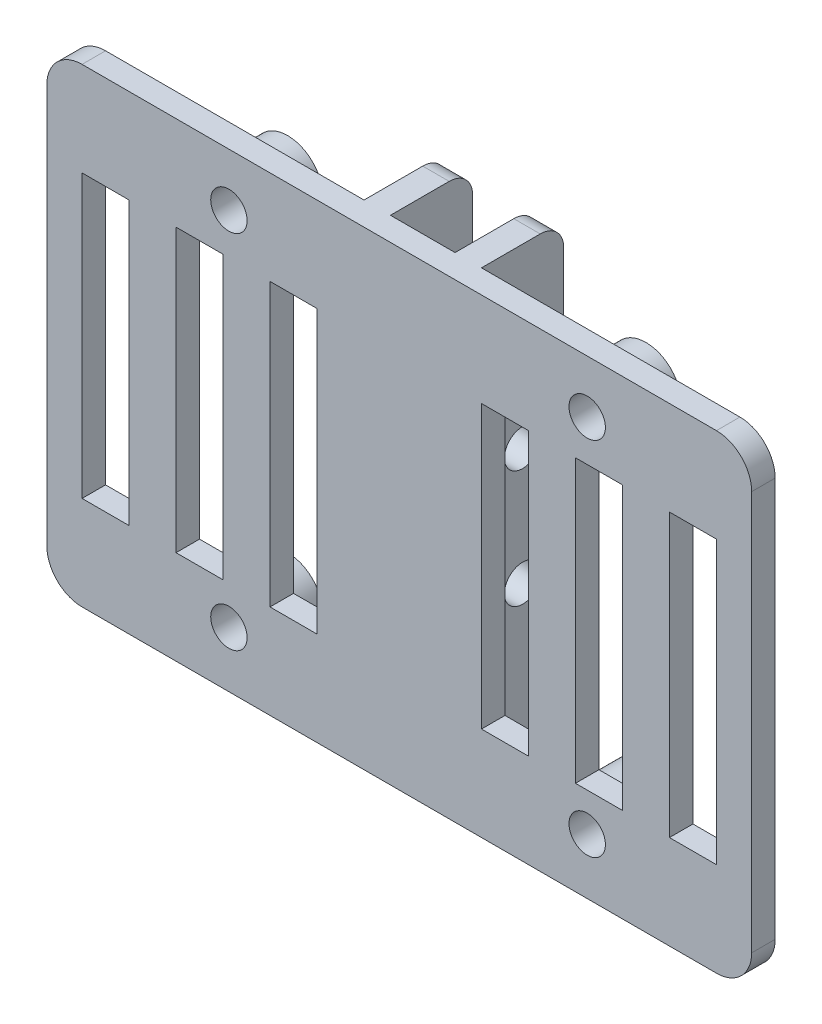
SolidWorks part; units mm, degrees
ref_plane "Plan de face" through (0, 0, 0) normal (0, 0, 1) x (1, 0, 0)
ref_plane "Plan de dessus" through (0, 0, 0) normal (0, 1, 0) x (1, 0, 0)
ref_plane "Plan de droite" through (0, 0, 0) normal (1, 0, 0) x (0, 0, -1)
sketch "Esquisse1" plane through (0, 0, 0) normal (0, 0, 1) x (1, 0, 0)
  line L1 (0, 0) -> (60, 0)
  line L2 (0, 0) -> (0, 40)
  line L3 (0, 40) -> (60, 40)
  line L4 (60, 0) -> (60, 40)
extrude "Boss.-Extru.1" add sketch "Esquisse1" along normal blind 9
sketch "Esquisse2" plane through (0, 0, 0) normal (0, 0, -1) x (-1, 0, 0)
  line L1 (-25, 40) -> (0, 40)
  line L2 (-25, 40) -> (-25, 0)
  line L3 (-25, 0) -> (0, 0)
  line L4 (0, 40) -> (0, 0)
  line L5 (-60, 40) -> (-35, 40)
  line L6 (-60, 40) -> (-60, 0)
  line L7 (-60, 0) -> (-35, 0)
  line L8 (-35, 40) -> (-35, 0)
  line L9 (-27.25, 40) -> (-32.75, 40)
  line L10 (-27.25, 40) -> (-27.25, 0)
  line L11 (-27.25, 0) -> (-32.75, 0)
  line L12 (-32.75, 40) -> (-32.75, 0)
  point P12 (0, 0)
  point P13 (0, 0)
  point P14 (0, 0)
  point P15 (0, 0)
  point P16 (0, 0)
  point P17 (0, 0)
  point P18 (0, 0)
extrude "Enlèv. mat.-Extru.1" cut sketch "Esquisse2" against normal blind 7
sketch "Esquisse3" plane through (35, 0, 0) normal (1, 0, 0) x (0, 0, -1)
  circle A0 centre (-3.5, 15) radius 1.55
  circle A1 centre (-3.5, 25) radius 1.55
extrude "Enlèv. mat.-Extru.2" cut sketch "Esquisse3" against normal through all
fillet "Congé1" radius 3 4 edges at (0, 0, 8) (60, 0, 8) (0, 40, 8) (60, 40, 8)
sketch "Esquisse9" plane through (0, 0, 7) normal (0, 0, -1) x (-1, 0, 0)
  circle A1 centre (-46, 35.5) radius 3
  circle A2 centre (-15.5, 35.5) radius 3
  circle A3 centre (-15.5, 4.75) radius 3
  circle A4 centre (-46, 4.75) radius 3
extrude "Boss.-Extru.2" add sketch "Esquisse9" along normal blind 3
sketch "Esquisse5" plane through (0, 0, 7) normal (0, 0, -1) x (-1, 0, 0)
  circle A0 centre (-46, 35.5) radius 1.55
  circle A1 centre (-46, 4.75) radius 1.55
  circle A2 centre (-15.5, 4.75) radius 1.55
  circle A3 centre (-15.5, 35.5) radius 1.55
extrude "Enlèv. mat.-Extru.4" cut sketch "Esquisse5" against normal through all both and the other way through all
sketch "Esquisse6" plane through (0, 0, 7) normal (0, 0, -1) x (-1, 0, 0)
  line L0 (-49, 32) -> (-45, 32)
  line L1 (-57, 32) -> (-53, 32)
  line L2 (-57, 32) -> (-57, 8)
  line L3 (-57, 8) -> (-53, 8)
  line L4 (-53, 32) -> (-53, 8)
  line L5 (-49, 32) -> (-49, 8)
  line L6 (-45, 32) -> (-45, 8)
  line L7 (-49, 8) -> (-45, 8)
  line L8 (-41, 32) -> (-37, 32)
  line L9 (-41, 32) -> (-41, 8)
  line L10 (-37, 32) -> (-37, 8)
  line L11 (-41, 8) -> (-37, 8)
  dimension "D1" = 3
sketch "Esquisse8" plane through (0, 0, 7) normal (0, 0, -1) x (-1, 0, 0)
  line L0 (-11, 32) -> (-11, 8)
  line L1 (-3, 32) -> (-7, 32)
  line L2 (-3, 32) -> (-3, 8)
  line L3 (-3, 8) -> (-7, 8)
  line L4 (-7, 32) -> (-7, 8)
  line L5 (-11, 32) -> (-15, 32)
  line L6 (-15, 32) -> (-15, 8)
  line L7 (-11, 8) -> (-15, 8)
  line L8 (-19, 32) -> (-19, 8)
  line L9 (-19, 32) -> (-23, 32)
  line L10 (-23, 32) -> (-23, 8)
  line L11 (-19, 8) -> (-23, 8)
  dimension "D1" = 3
extrude "Enlèv. mat.-Extru.5" cut sketch "Esquisse8" against normal blind 7
extrude "Enlèv. mat.-Extru.6" cut sketch "Esquisse6" against normal blind 7
fillet "Congé2" radius 2 4 edges at (33.875, 0, 0) (26.125, 0, 0) (26.125, 40, 0) (33.875, 40, 0)
